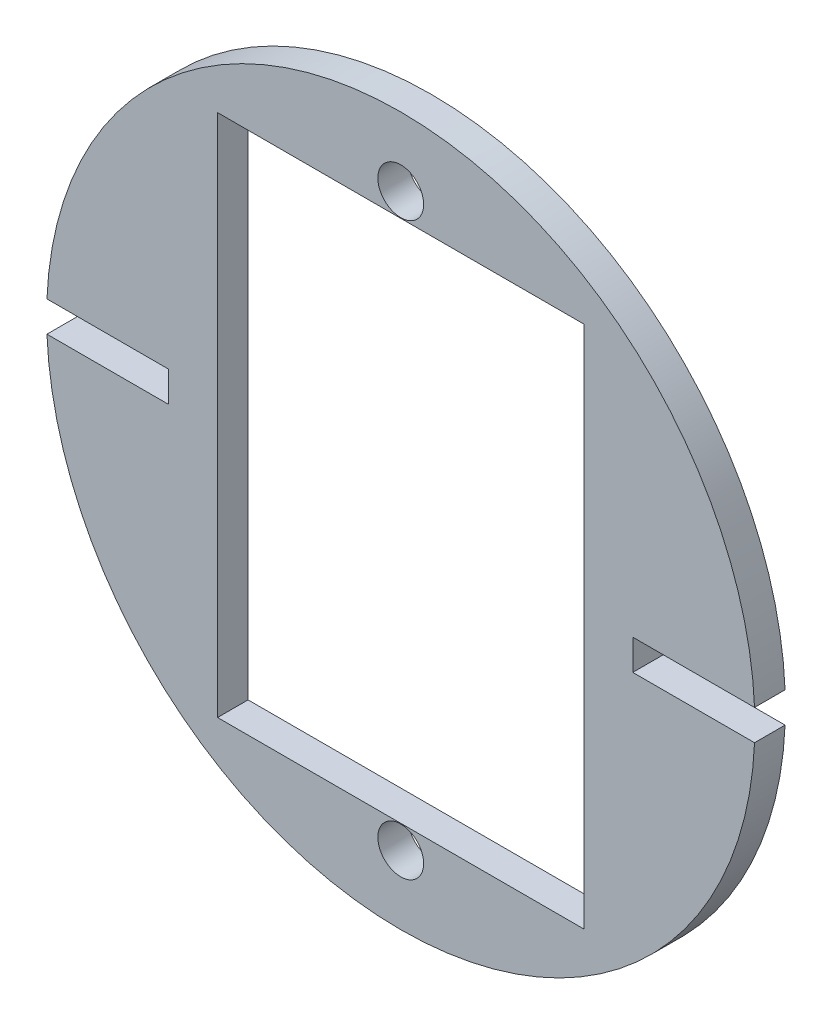
SolidWorks part; units mm, degrees
material "E-Glass Fiber"
ref_plane "Front Plane" through (0, 0, 0) normal (0, 0, 1) x (1, 0, 0)
ref_plane "Top Plane" through (0, 0, 0) normal (0, 1, 0) x (1, 0, 0)
ref_plane "Right Plane" through (0, 0, 0) normal (1, 0, 0) x (0, 0, -1)
sketch "Sketch1" plane through (0, 0, 0) normal (0, 0, 1) x (1, 0, 0)
  circle A0 centre (0, 0) radius 73.66
  dimension "D1" = 147.32
extrude "Boss-Extrude1" add sketch "Sketch1" along normal blind 6.35
sketch "Sketch2" plane through (0, 0, 0) normal (0, 0, -1) x (-1, 0, 0)
  line L0 (-76.2, 0) -> (73.66, 0) construction
  line L1 (-48.26, 0) -> (-48.26, 3.175)
  line L2 (-48.26, 3.175) -> (-76.2, 3.175)
  line L3 (-76.2, 3.175) -> (-76.2, -3.175)
  line L4 (-76.2, -3.175) -> (-48.26, -3.175)
  line L5 (-48.26, -3.175) -> (-48.26, 0)
  line L6 (0, 35.7336) -> (0, -26.6213) construction
  line L7 (48.26, -3.175) -> (48.26, 0)
  line L8 (48.26, 0) -> (48.26, 3.175)
  line L9 (76.2, -3.175) -> (48.26, -3.175)
  line L10 (76.2, 3.175) -> (76.2, -3.175)
  line L11 (48.26, 3.175) -> (76.2, 3.175)
  circle A0 centre (0, 0) radius 73.66 construction
  point P21 (-48.26, 1.5875)
  dimension "D1" = 6.35
  dimension "D2" = 27.94
  dimension "D3" = 48.26
extrude "Cut-Extrude1" cut sketch "Sketch2" against normal through all
sketch "Sketch3" plane through (0, 0, 0) normal (0, 0, -1) x (-1, 0, 0)
  line L0 (-73.93, 0) -> (73.5325, 0) construction
  line L1 (0, 73.66) -> (0, -73.66) construction
  line L3 (-38.1, 54.61) -> (38.1, 54.61)
  line L4 (-38.1, 54.61) -> (-38.1, -54.61)
  line L5 (-38.1, -54.61) -> (38.1, -54.61)
  line L6 (38.1, 54.61) -> (38.1, -54.61)
  line L7 (-38.1, 54.61) -> (38.1, -54.61) construction
  line L8 (-38.1, -54.61) -> (38.1, 54.61) construction
  arc A0 (73.5915, 3.175) -> (-73.5915, 3.175) centre (0, 0) ccw construction
  arc A1 (-73.5915, -3.175) -> (73.5915, -3.175) centre (0, 0) ccw construction
  point P11 (0, 0)
sketch "Sketch4" plane through (0, 0, 0) normal (0, 0, -1) x (-1, 0, 0)
  line L0 (47.625, 0) -> (73.5325, 0) construction
  line L2 (0, 73.66) -> (0, -73.66) construction
  line L3 (-73.93, 0) -> (38.1, 0) construction
  line L4 (0, 0) -> (38.1, 0)
  line L5 (38.1, 54.61) -> (38.1, -54.61) construction
  line L7 (0, 73.66) -> (0, -54.61) construction
  line L8 (0, -64.135) -> (0, -73.66) construction
  circle A0 centre (0, -59.3725) radius 4.7625
  circle A1 centre (0, 59.3725) radius 4.7625
  circle A2 centre (42.8625, 0) radius 4.7625
  circle A3 centre (-42.8625, 0) radius 4.7625
extrude "Cut-Extrude2" cut sketch "Sketch4" against normal through all contours A0 | A1
sketch "Sketch5" plane through (0, 0, 0) normal (0, 0, -1) x (-1, 0, 0)
  line L0 (0, 0) -> (0, 54.483) construction
  line L1 (0, 0) -> (38.1, 0) construction
  line L2 (-38.1, 54.483) -> (38.1, 54.483)
  line L3 (38.1, 54.483) -> (38.1, -54.483)
  line L4 (-38.1, -54.483) -> (38.1, -54.483)
  line L5 (-38.1, 54.483) -> (-38.1, -54.483)
  point P8 (0, -54.483)
extrude "Cut-Extrude5" cut sketch "Sketch5" against normal through all
